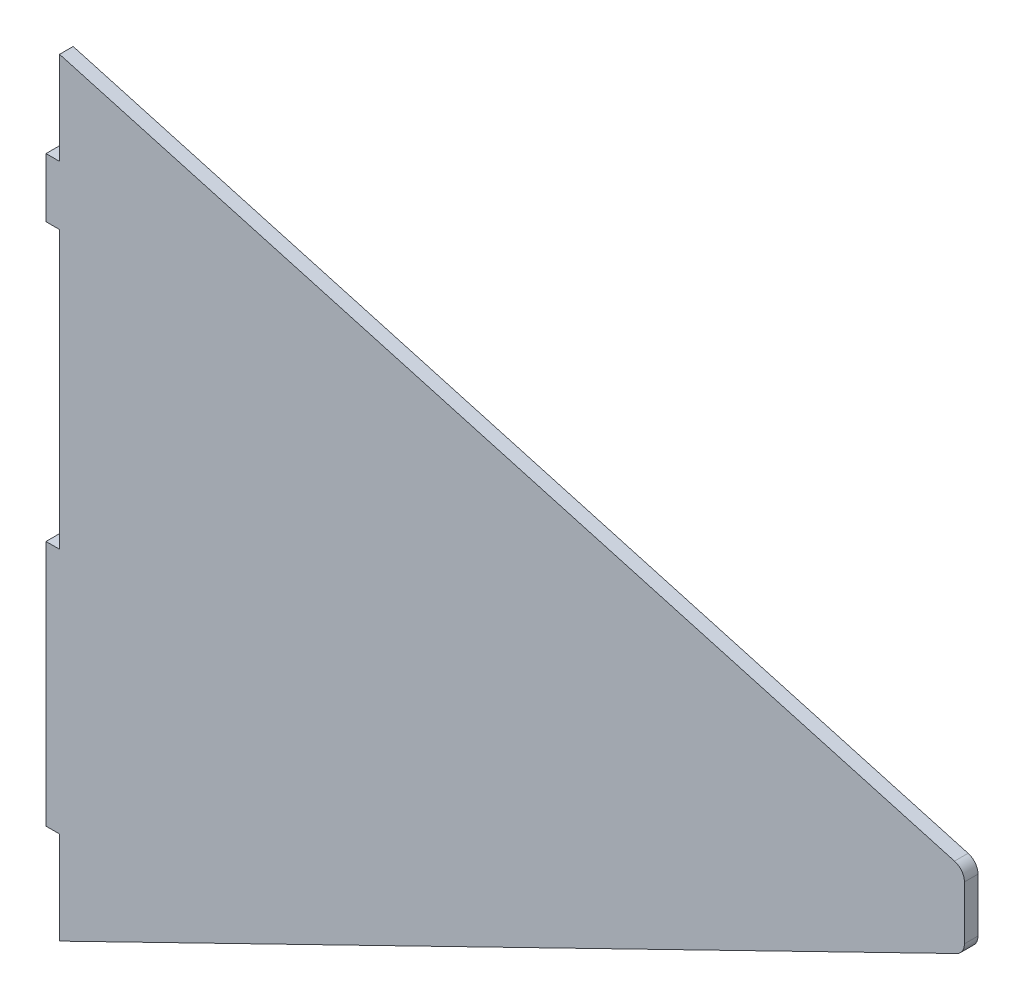
SolidWorks part; units mm, degrees
ref_plane "Front Plane" through (0, 0, 0) normal (0, 0, 1) x (1, 0, 0)
ref_plane "Top Plane" through (0, 0, 0) normal (0, 1, 0) x (1, 0, 0)
ref_plane "Right Plane" through (0, 0, 0) normal (1, 0, 0) x (0, 0, -1)
sketch "Sketch1" plane through (0, 0, 0) normal (0, 0, 1) x (1, 0, 0)
  line L0 (203, -32.85) -> (3, 23.3)
  line L2 (3, 23.3) -> (3, 2.8)
  line L3 (3, 2.8) -> (0, 2.8)
  line L4 (0, 2.8) -> (0, -10.25)
  line L5 (0, -10.25) -> (3, -10.25)
  line L6 (3, -10.25) -> (3, -71.45)
  line L7 (3, -71.45) -> (0, -71.45)
  line L8 (0, -71.45) -> (0, -125.95)
  line L9 (0, -125.95) -> (3, -125.95)
  line L10 (3, -125.95) -> (3, -146.45)
  line L11 (3, -146.45) -> (203, -48.85)
  line L13 (203, -48.85) -> (203, -32.85)
  line L14 (0, -48.85) -> (1100, -48.85) construction
  line L15 (1100, -32.85) -> (0, -32.85) construction
  line L16 (0, 3.3) -> (3, 3.3) construction
  line L17 (0, -10.75) -> (3, -10.75) construction
  line L18 (0, -70.95) -> (3, -70.95) construction
  line L19 (0, -126.45) -> (3, -126.45) construction
  point P24 (1.5, -10.75)
  dimension "D1" = 0.5
  dimension "D2" = 0.5
  dimension "D3" = 0.5
  dimension "D4" = 0.5
  dimension "D5" = 200
extrude "Boss-Extrude1" add sketch "Sketch1" along normal blind 3
fillet "Fillet1" radius 3 2 edges at (203, -32.85, 1.5) (203, -48.85, 1.5)
